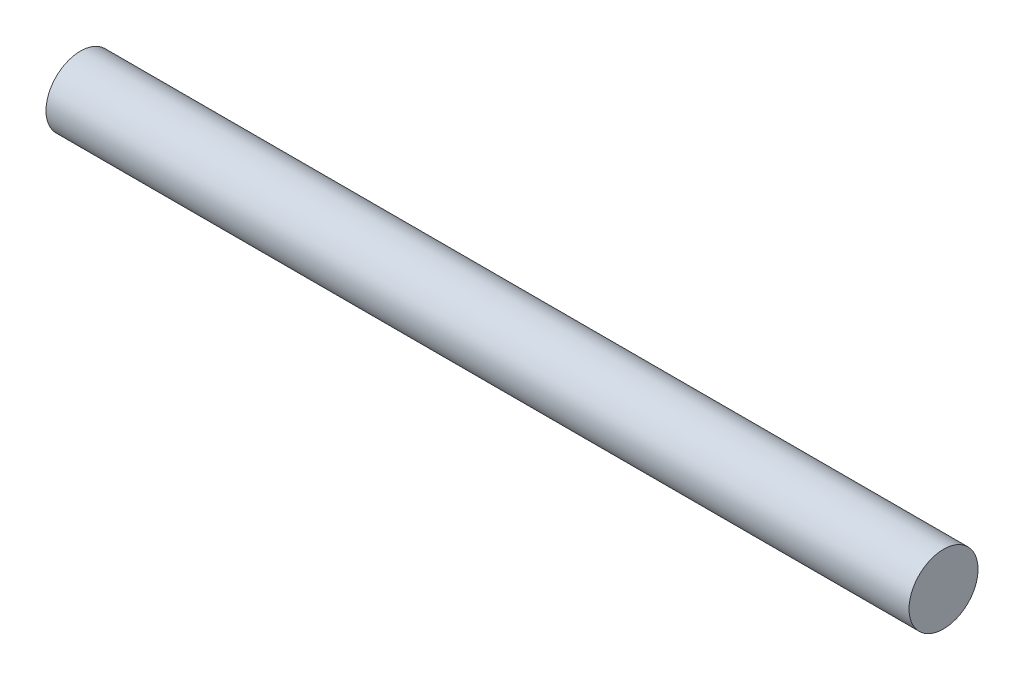
SolidWorks part; units mm, degrees
ref_plane "Plan de face" through (0, 0, 0) normal (0, 0, 1) x (1, 0, 0)
ref_plane "Plan de dessus" through (0, 0, 0) normal (0, 1, 0) x (1, 0, 0)
ref_plane "Plan de droite" through (0, 0, 0) normal (1, 0, 0) x (0, 0, -1)
sketch "Esquisse1" plane through (0, 0, 0) normal (0, 0, 1) x (1, 0, 0)
  line L1 (0, 0) -> (100, 0)
  line L2 (0, 0) -> (0, 4)
  line L3 (0, 4) -> (100, 4)
  line L4 (100, 0) -> (100, 4)
  dimension "D1" = 4
  dimension "D2" = 100
revolve "Révolution1" add sketch "Esquisse1" angle 360 about L1
